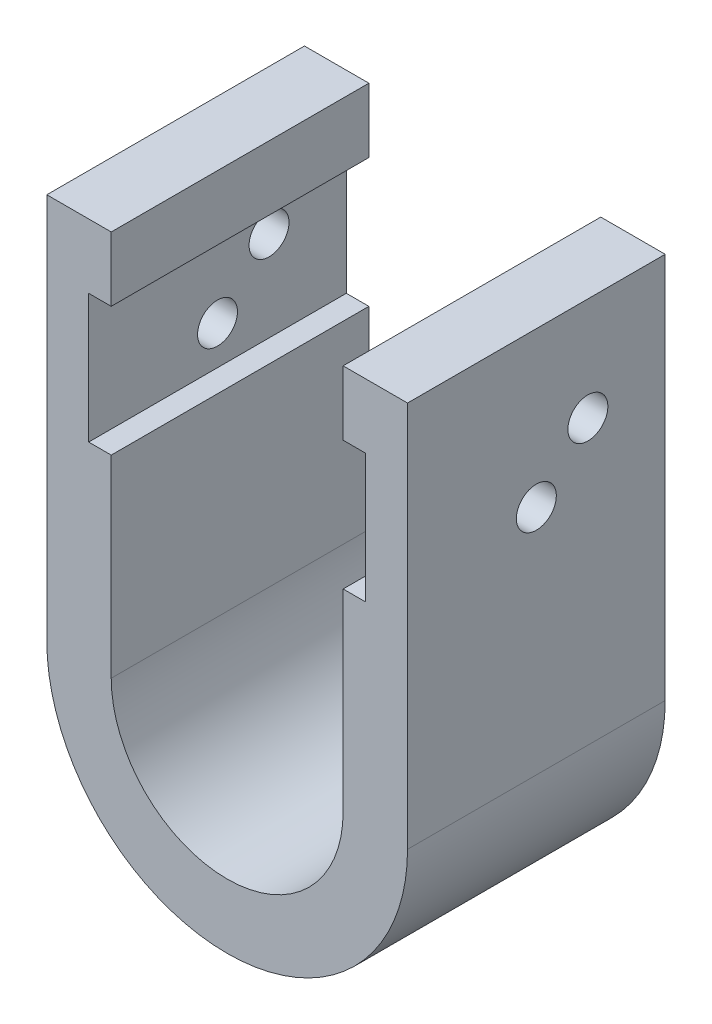
SolidWorks part; units mm, degrees
ref_plane "前视基准面" through (0, 0, 0) normal (0, 0, 1) x (1, 0, 0)
ref_plane "上视基准面" through (0, 0, 0) normal (0, 1, 0) x (1, 0, 0)
ref_plane "右视基准面" through (0, 0, 0) normal (1, 0, 0) x (0, 0, -1)
sketch "草图1" plane through (0, 0, 0) normal (0, 0, 1) x (1, 0, 0)
  line L0 (0, 0) -> (-21.9163, 0) construction
  line L1 (-14, 0) -> (-14, 30)
  line L2 (-14, 30) -> (-9, 30)
  line L3 (14, 30) -> (14, 0)
  line L4 (-9, 0) -> (-9, 30)
  line L6 (9, 30) -> (9, 0)
  line L7 (9, 30) -> (14, 30)
  arc A1 (-9, 0) -> (9, 0) centre (0, 0) ccw
  arc A2 (-14, 0) -> (14, 0) centre (0, 0) ccw
  dimension "D1" = 18
  dimension "D2" = 5
  dimension "D3" = 30
extrude "凸台-拉伸1" add sketch "草图1" along normal blind 20
sketch "草图2" plane through (14, 0, 0) normal (1, 0, 0) x (0, 0, -1)
  line L0 (-20, 0) -> (-20, 30) construction
  line L3 (-20, 30) -> (0, 30) construction
  circle A0 centre (-10, 18) radius 1.55
  circle A1 centre (-6, 22) radius 1.55
  dimension "D5" = 3.1
  dimension "D6" = 3.1
  dimension "D1" = 10
  dimension "D2" = 4
  dimension "D3" = 8
  dimension "D4" = 14
extrude "切除-拉伸1" cut sketch "草图2" against normal blind 30
sketch "草图3" plane through (0, 0, 0) normal (0, 0, -1) x (-1, 0, 0)
  line L0 (-9, 25) -> (-10.75, 25)
  line L1 (-9, 30) -> (-9, 0) construction
  line L2 (-10.75, 25) -> (-10.75, 15)
  line L3 (-10.75, 15) -> (-9, 15)
  line L4 (-9, 15) -> (-9, 25)
  line L5 (-14, 30) -> (-9, 30) construction
  dimension "D1" = 5
  dimension "D2" = 10
  dimension "D3" = 1.75
extrude "切除-拉伸2" cut sketch "草图3" against normal up to next (20 mm away)
mirror "镜向1" about plane through (0, 0, 0) normal (1, 0, 0) of "切除-拉伸2"
